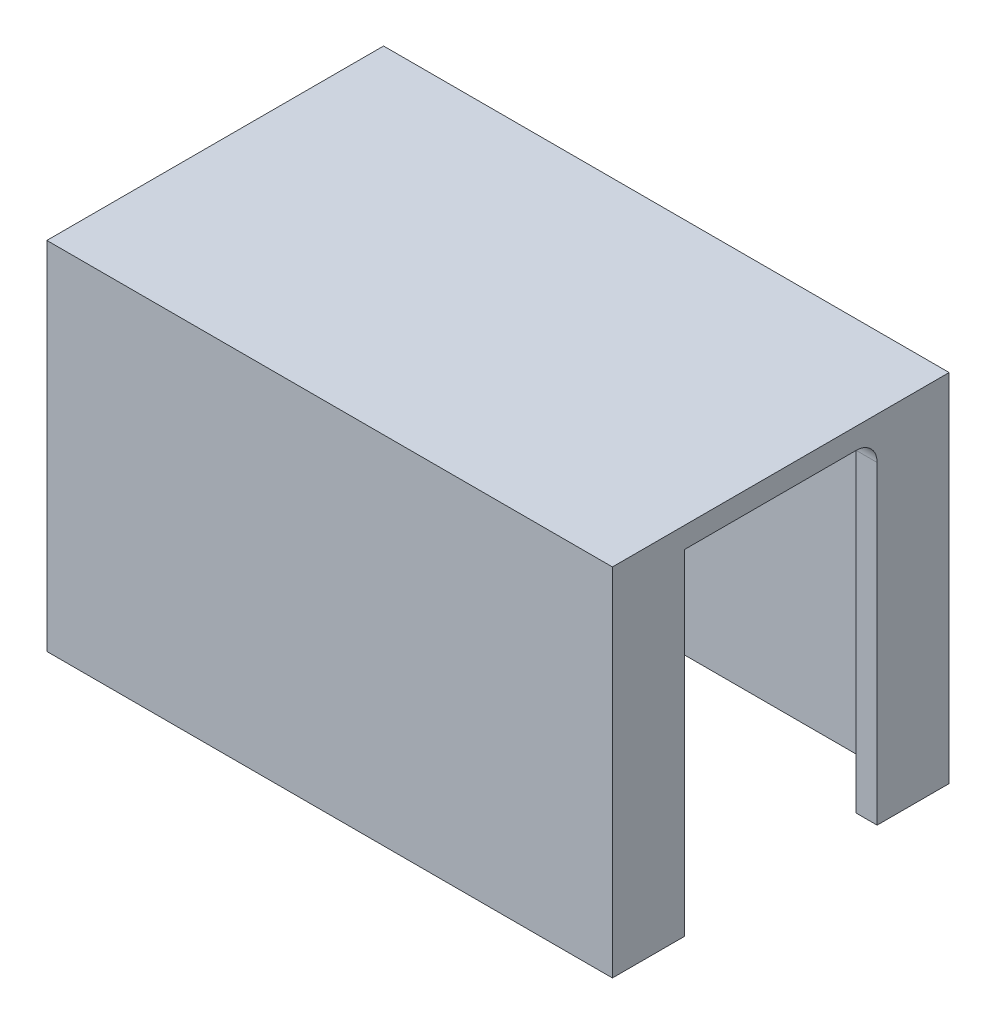
SolidWorks part; units mm, degrees
ref_plane "Front Plane" through (0, 0, 0) normal (0, 0, 1) x (1, 0, 0)
ref_plane "Top Plane" through (0, 0, 0) normal (0, 1, 0) x (1, 0, 0)
ref_plane "Right Plane" through (0, 0, 0) normal (1, 0, 0) x (0, 0, -1)
ref_plane "Plane1" through (0, 0, 0) normal (0, 0, -1) x (-1, 0, 0)
sketch "Sketch1" plane through (0, 0, 0) normal (0, 0, -1) x (-1, 0, 0)
  line L0 (-85.7504, 0) -> (0, 0)
  line L1 (0, 0) -> (0, 53.975)
  line L2 (0, 53.975) -> (-85.7504, 53.975)
  line L3 (-85.7504, 53.975) -> (-85.7504, 0)
extrude "Boss-Extrude1" add sketch "Sketch1" against normal blind 51.054
sketch "Sketch2" plane through (0, 0, 0) normal (-1, 0, 0) x (0, 0, 1)
  line L0 (40.132, 0) -> (40.132, 50.8)
  line L1 (40.132, 50.8) -> (10.922, 50.8)
  line L2 (10.922, 50.8) -> (10.922, 0)
  line L3 (10.922, 0) -> (40.132, 0)
extrude "Cut-Extrude1" cut sketch "Sketch2" against normal through all
sketch "Sketch3" plane through (0, 0, 10.922) normal (0, 0, 1) x (1, 0, 0)
  line L0 (3.175, 50.8) -> (3.175, 0)
  line L1 (3.175, 0) -> (82.5754, 0)
  line L2 (82.5754, 0) -> (82.5754, 50.8)
  line L3 (82.5754, 50.8) -> (3.175, 50.8)
extrude "Cut-Extrude2" cut sketch "Sketch3" against normal blind 7.747
sketch "Sketch4" plane through (0, 0, 0) normal (0, -1, 0) x (1, 0, 0)
  line L0 (82.5754, 47.879) -> (3.175, 47.879)
  line L1 (3.175, 47.879) -> (3.175, 40.132)
  line L2 (3.175, 40.132) -> (82.5754, 40.132)
  line L3 (82.5754, 40.132) -> (82.5754, 47.879)
extrude "Cut-Extrude3" cut sketch "Sketch4" against normal blind 50.8
fillet "Fillet2" radius 3.175 1 edges at (3.175, 25.4, 3.175)
fillet "Fillet3" radius 3.175 3 edges at (44.4627, 50.8, 3.175) (4.1049, 50.8, 4.1049) (3.175, 50.8, 8.636)
fillet "Fillet4" radius 3.175 1 edges at (3.175, 50.8, 10.922)
fillet "Fillet5" radius 3.175 3 edges at (82.5754, 50.8, 8.636) (82.5754, 49.8701, 4.1049) (82.5754, 23.8125, 3.175)
fillet "Fillet6" radius 3.175 1 edges at (82.5754, 50.8, 10.922)
